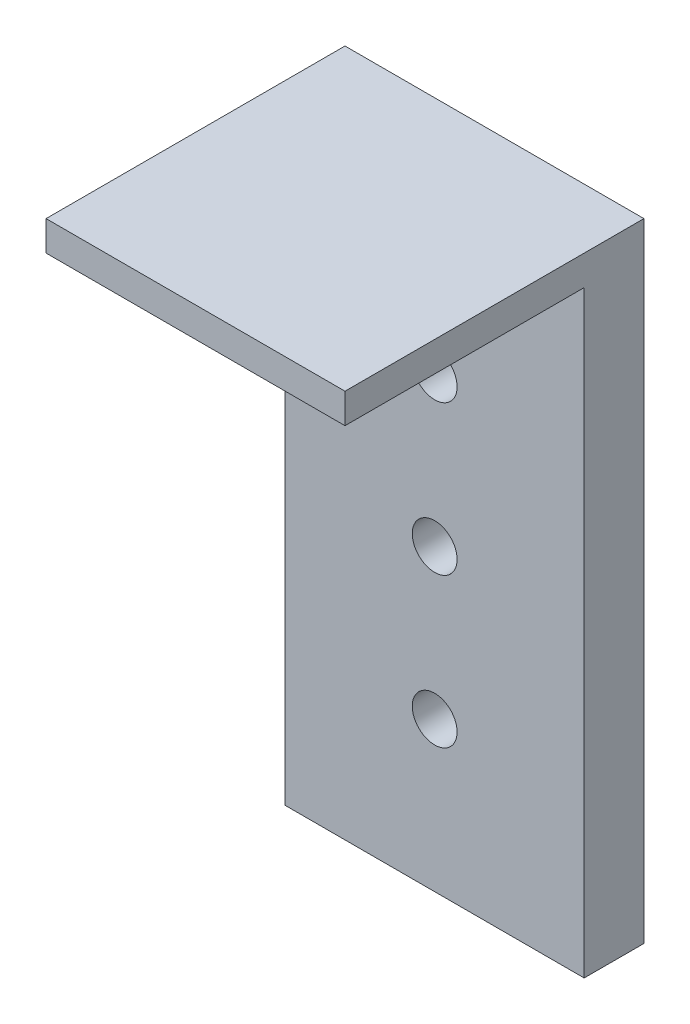
SolidWorks part; units mm, degrees
ref_plane "Front Plane" through (0, 0, 0) normal (0, 0, 1) x (1, 0, 0)
ref_plane "Top Plane" through (0, 0, 0) normal (0, 1, 0) x (1, 0, 0)
ref_plane "Right Plane" through (0, 0, 0) normal (1, 0, 0) x (0, 0, -1)
sketch "Sketch1" plane through (0, 0, 0) normal (0, 0, 1) x (1, 0, 0)
  line L0 (5, 9.7151) -> (5, 14.7151) construction
  line L5 (0, 9.7151) -> (10, 9.7151)
  line L6 (0, 9.7151) -> (0, 29.7151)
  line L7 (0, 29.7151) -> (10, 29.7151)
  line L8 (10, 9.7151) -> (10, 29.7151)
  line L9 (5, 14.7151) -> (5, 19.7151) construction
  line L10 (5, 19.7151) -> (5, 24.7151) construction
sketch "Sketch2" plane through (0, 0, 0) normal (0, 0, 1) x (1, 0, 0)
  line L0 (5, 9.7151) -> (5, 14.7151) construction
  line L1 (5, 14.7151) -> (5, 19.7151) construction
  line L2 (5, 19.7151) -> (5, 24.7151) construction
  circle A0 centre (5, 24.7151) radius 0.75
  circle A1 centre (5, 19.7151) radius 0.75
  circle A2 centre (5, 14.7151) radius 0.75
  point P11 (5, 19.2953)
  point P13 (5.4184, 14.7151)
extrude "Boss-Extrude1" add sketch "Sketch1" along normal blind 2
extrude "Cut-Extrude2" cut sketch "Sketch2" along normal blind 2
sketch "Sketch5" plane through (0, 29.7151, 0) normal (0, 1, 0) x (1, 0, 0)
  line L1 (0, 0) -> (10, 0)
  line L2 (0, 0) -> (0, -10)
  line L3 (0, -10) -> (10, -10)
  line L4 (10, 0) -> (10, -10)
extrude "Boss-Extrude2" add sketch "Sketch5" along normal blind 1
ref_plane "Plane1" through (0, 29.7151, 0) normal (0, -1, 0) x (-1, 0, 0)
